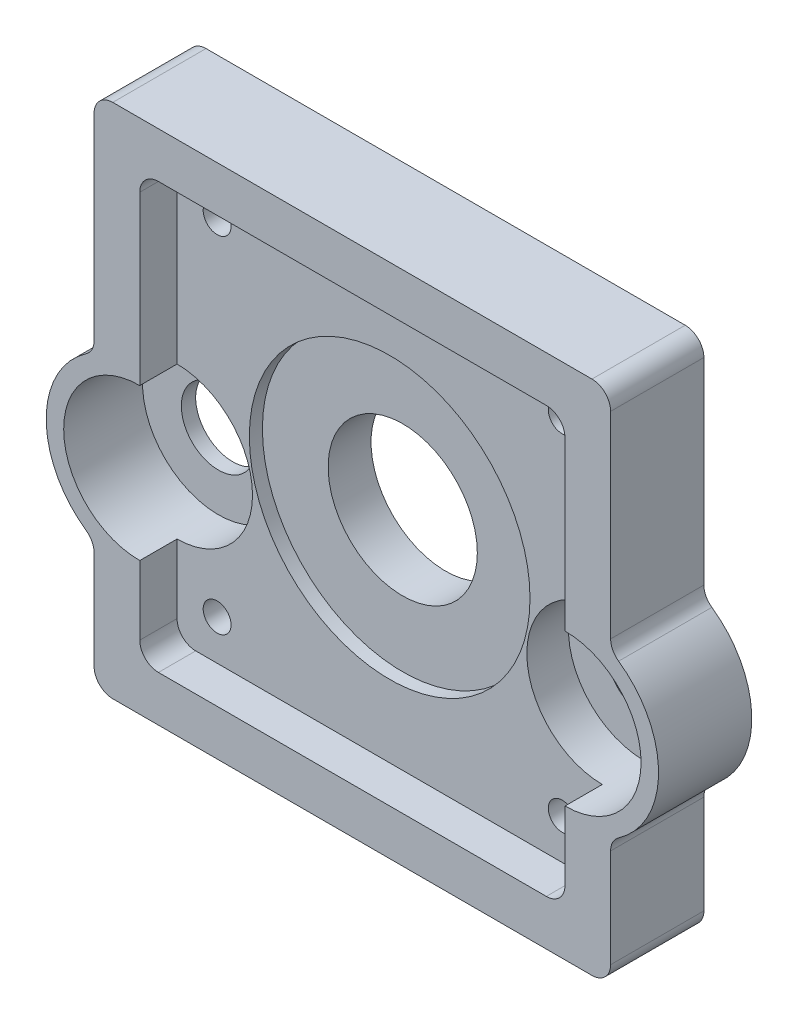
SolidWorks part; units mm, degrees
ref_plane "Front Plane" through (0, 0, 0) normal (0, 0, 1) x (1, 0, 0)
ref_plane "Top Plane" through (0, 0, 0) normal (0, 1, 0) x (1, 0, 0)
ref_plane "Right Plane" through (0, 0, 0) normal (1, 0, 0) x (0, 0, -1)
sketch "Sketch1" plane through (0, 0, 0) normal (0, 0, 1) x (1, 0, 0)
  line L0 (0, 0) -> (0, -6.708) construction
  line L1 (-35.1736, -35.1736) -> (35.1736, -35.1736)
  line L2 (-35.1736, -35.1736) -> (-35.1736, -17.8065)
  line L3 (-35.1736, 35.1736) -> (35.1736, 35.1736)
  line L4 (35.1736, -35.1736) -> (35.1736, -17.8065)
  line L5 (-35.1736, -35.1736) -> (35.1736, 35.1736) construction
  line L6 (-35.1736, 35.1736) -> (35.1736, -35.1736) construction
  line L7 (-29, -6.708) -> (29, -6.708) construction
  line L8 (-35.1736, 4.3905) -> (-35.1736, 35.1736)
  line L9 (35.1736, 4.3905) -> (35.1736, 35.1736)
  arc A0 (-35.1736, 4.3905) -> (-35.1736, -17.8065) centre (-29, -6.708) ccw
  arc A1 (35.1736, -17.8065) -> (35.1736, 4.3905) centre (29, -6.708) ccw
  point P0 (0, 0)
  point P11 (0, -6.708)
  dimension "D4" = 25.4
  dimension "D1" = 70.3472
  dimension "D2" = 6.708
  dimension "D3" = 58
extrude "Boss-Extrude1" add sketch "Sketch1" along normal blind 12.7
sketch "Sketch16" plane through (0, 0, 12.7) normal (0, 0, 1) x (1, 0, 0)
  line L0 (-35.1736, 35.1736) -> (35.1736, -35.1736) construction
  circle A0 centre (0, 0) radius 10.16
  dimension "D1" = 20.32
extrude "Cut-Extrude3" cut sketch "Sketch16" against normal through all and the other way through all
sketch "Sketch17" plane through (0, 0, 12.7) normal (0, 0, 1) x (1, 0, 0)
  line L0 (-35.1736, 35.1736) -> (35.1736, -35.1736) construction
  line L2 (-28.956, -28.956) -> (28.956, -28.956)
  line L3 (-28.956, -28.956) -> (-28.956, 28.956)
  line L4 (-28.956, 28.956) -> (28.956, 28.956)
  line L5 (28.956, -28.956) -> (28.956, 28.956)
  line L6 (-28.956, -28.956) -> (28.956, 28.956) construction
  line L7 (-28.956, 28.956) -> (28.956, -28.956) construction
  point P4 (0, 0)
  dimension "D1" = 57.912
extrude "Cut-Extrude4" cut sketch "Sketch17" against normal blind 5.08
hole_wizard "CBORE for 3/8 Binding Head Machine Screw1" positions "Sketch18" profile "Sketch20" counterbore size "3/8" standard "ANSI Inch" end condition through all
sketch "Sketch18" plane through (0, 0, 12.7) normal (0, 0, 1) x (1, 0, 0)
  line L0 (35.1736, 4.3905) -> (35.1736, 35.1736) construction
  line L1 (35.1736, 35.1736) -> (-35.1736, 35.1736) construction
  circle A0 centre (0, 0) radius 10.16 construction
  point P49 (-29, -6.708)
  point P52 (29, -6.708)
  dimension "D1" = 29
  dimension "D2" = 64.1736
  dimension "D3" = 41.8816
sketch "Sketch20" plane through (-29, -6.708, 12.7) normal (1, 0, 0) x (0, -1, 0)
  line L0 (0, 0) -> (0, 12.7)
  line L1 (0, 12.7) -> (5.0419, 12.7)
  line L3 (5.0419, 12.7) -> (5.0419, 10.7442)
  line L4 (5.0419, 10.7442) -> (10.3187, 10.7442)
  line L5 (10.3187, 10.7442) -> (10.3187, 0)
  line L7 (10.3187, 0) -> (0, 0)
  line L11 (0, -6.35) -> (0, 107.95) construction
  dimension "Thru Hole Dia." = 10.0838
  dimension "Thru Hole Depth" = 12.7
  dimension "C'Bore Dia." = 20.6375
  dimension "C'Bore Depth" = 10.7442
fillet "Fillet3" radius 2.54 8 edges at (28.956, -28.956, 10.16) (-28.956, -28.956, 10.16) (28.956, 28.956, 10.16) (-28.956, 28.956, 10.16) (-35.1736, -35.1736, 6.35) (35.1736, -35.1736, 6.35) (35.1736, 35.1736, 6.35) (-35.1736, 35.1736, 6.35)
hole_wizard "Tap Drill for #10-24 Tap1" positions "Sketch21" profile "Sketch23" hole size "#10-24" standard "ANSI Inch" end condition through all
sketch "Sketch21" plane through (0, 0, 7.62) normal (0, 0, 1) x (1, 0, 0)
  line L7 (28.956, 3.6107) -> (28.956, 26.416) construction
  line L8 (-26.416, -28.956) -> (26.416, -28.956) construction
  line L9 (-34.4296, 34.4296) -> (34.4296, -34.4296) construction
  line L12 (-23.5, -23.5) -> (23.5, -23.5) construction
  line L13 (-23.5, -23.5) -> (-23.5, 23.5) construction
  line L14 (-23.5, 23.5) -> (23.5, 23.5) construction
  line L15 (23.5, -23.5) -> (23.5, 23.5) construction
  line L16 (-23.5, -23.5) -> (23.5, 23.5) construction
  line L17 (-23.5, 23.5) -> (23.5, -23.5) construction
  arc A0 (-32.6336, 35.1736) -> (-35.1736, 32.6336) centre (-32.6336, 32.6336) ccw construction
  arc A1 (32.6336, -35.1736) -> (35.1736, -32.6336) centre (32.6336, -32.6336) ccw construction
  point P109 (-23.5, 23.5)
  point P112 (23.5, 23.5)
  point P115 (23.5, -23.5)
  point P118 (-23.5, -23.5)
  dimension "D1" = 47
  dimension "D2" = 47
sketch "Sketch23" plane through (-23.5, -23.5, 7.62) normal (1, 0, 0) x (0, -1, 0)
  line L0 (0, 0) -> (0, 7.62)
  line L1 (0, 7.62) -> (1.8986, 7.62)
  line L2 (1.8986, 7.62) -> (1.8986, 0)
  line L5 (1.8986, 0) -> (0, 0)
  line L11 (0, -6.35) -> (0, 107.95) construction
  dimension "Thru Hole Dia." = 3.7973
  dimension "Thru Hole Depth" = 7.62
thread "Thread1" pitch 1.0583 start angle 0, offset 0, length 0, pitch 1.0583, diameter 3.7973
ref_plane "Plane1" through (-21.6014, 23.5, 0) normal (0, -1, 0) x (1, 0, 0)
sketch "Thread Profile1" plane through (-21.6014, 23.5, 0) normal (0, -1, 0) x (1, 0, 0)
  line L0 (0, 0) -> (0, 1.0583) construction
  line L11 (0, 0) -> (0, 0.926)
  line L12 (0, 0.926) -> (-0.5728, 0.5953)
  line L13 (-0.5728, 0.5953) -> (-0.5728, 0.3307)
  line L15 (-0.5728, 0.3307) -> (0, 0)
  line L17 (-0.5728, 0.463) -> (0, 0.463) construction
  point P2 (0, 0)
  dimension "Pitch" = 1.0583
  dimension "Profile_Angle" = 60
  dimension "Profile_Land" = 0.2646
  dimension "Profile_Height" = 0.5728
thread "Thread2" pitch 1.0583 start angle 0, offset 0, length 0, pitch 1.0583, diameter 3.7973
ref_plane "Plane2" through (25.3987, 23.5, 0) normal (0, -1, 0) x (1, 0, 0)
sketch "Thread Profile2" plane through (25.3987, 23.5, 0) normal (0, -1, 0) x (1, 0, 0)
  line L0 (0, 0) -> (0, 1.0583) construction
  line L11 (0, 0) -> (0, 0.926)
  line L12 (0, 0.926) -> (-0.5728, 0.5953)
  line L13 (-0.5728, 0.5953) -> (-0.5728, 0.3307)
  line L15 (-0.5728, 0.3307) -> (0, 0)
  line L17 (-0.5728, 0.463) -> (0, 0.463) construction
  point P2 (0, 0)
  dimension "Pitch" = 1.0583
  dimension "Profile_Angle" = 60
  dimension "Profile_Land" = 0.2646
  dimension "Profile_Height" = 0.5728
thread "Thread3" pitch 1.0583 start angle 0, offset 0, length 0, pitch 1.0583, diameter 3.7973
ref_plane "Plane3" through (25.3987, -23.5, 0) normal (0, -1, 0) x (1, 0, 0)
sketch "Thread Profile3" plane through (25.3987, -23.5, 0) normal (0, -1, 0) x (1, 0, 0)
  line L0 (0, 0) -> (0, 1.0583) construction
  line L11 (0, 0) -> (0, 0.926)
  line L12 (0, 0.926) -> (-0.5728, 0.5953)
  line L13 (-0.5728, 0.5953) -> (-0.5728, 0.3307)
  line L15 (-0.5728, 0.3307) -> (0, 0)
  line L17 (-0.5728, 0.463) -> (0, 0.463) construction
  point P2 (0, 0)
  dimension "Pitch" = 1.0583
  dimension "Profile_Angle" = 60
  dimension "Profile_Land" = 0.2646
  dimension "Profile_Height" = 0.5728
thread "Thread4" pitch 1.0583 start angle 0, offset 0, length 0, pitch 1.0583, diameter 3.7973
ref_plane "Plane4" through (-21.6014, -23.5, 0) normal (0, -1, 0) x (1, 0, 0)
sketch "Thread Profile4" plane through (-21.6014, -23.5, 0) normal (0, -1, 0) x (1, 0, 0)
  line L0 (0, 0) -> (0, 1.0583) construction
  line L11 (0, 0) -> (0, 0.926)
  line L12 (0, 0.926) -> (-0.5728, 0.5953)
  line L13 (-0.5728, 0.5953) -> (-0.5728, 0.3307)
  line L15 (-0.5728, 0.3307) -> (0, 0)
  line L17 (-0.5728, 0.463) -> (0, 0.463) construction
  point P2 (0, 0)
  dimension "Pitch" = 1.0583
  dimension "Profile_Angle" = 60
  dimension "Profile_Land" = 0.2646
  dimension "Profile_Height" = 0.5728
sketch "Sketch24" plane through (0, 0, 7.62) normal (0, 0, 1) x (1, 0, 0)
  circle A0 centre (0, 0) radius 19.1135
  dimension "D1" = 38.227
extrude "Cut-Extrude5" cut sketch "Sketch24" against normal blind 1.778
fillet "Fillet4" radius 2.54 4 edges at (-35.1736, 4.3905, 6.35) (-35.1736, -17.8065, 6.35) (35.1736, -17.8065, 6.35) (35.1736, 4.3905, 6.35)
